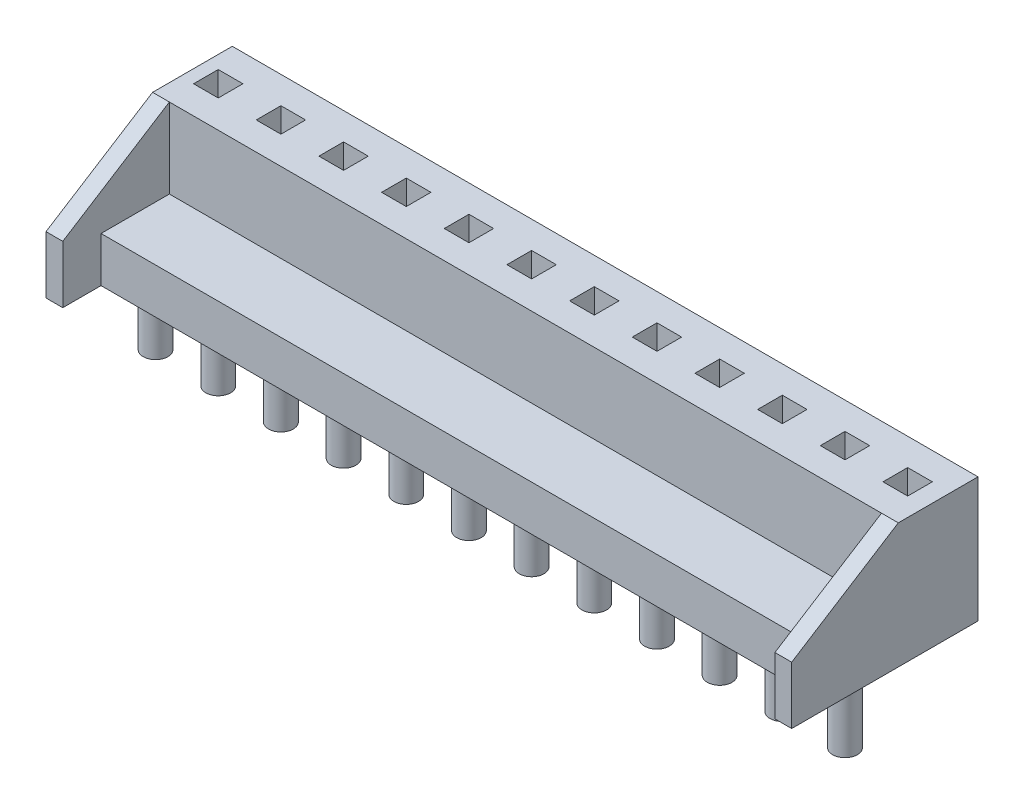
SolidWorks part; units mm, degrees
ref_plane "Front Plane" through (0, 0, 0) normal (0, 0, 1) x (1, 0, 0)
ref_plane "Top Plane" through (0, 0, 0) normal (0, 1, 0) x (1, 0, 0)
ref_plane "Right Plane" through (0, 0, 0) normal (1, 0, 0) x (0, 0, -1)
sketch "Sketch1" plane through (0, 0, 0) normal (1, 0, 0) x (0, 0, -1)
  line L0 (-2.77, 0) -> (3.23, 0)
  line L1 (3.23, 0) -> (3.23, 5.06)
  line L2 (3.23, 5.06) -> (0, 5.06)
  line L3 (0, 5.06) -> (0, 1.83)
  line L4 (0, 1.83) -> (-2.77, 1.83)
  line L5 (-2.77, 1.83) -> (-2.77, 0)
  dimension "D1" = 6
  dimension "D2" = 3.23
  dimension "D3" = 5.06
  dimension "D4" = 1.83
extrude "Boss-Extrude1" add sketch "Sketch1" along normal mid plane 30.22 contours L4 L5 L0 L1 L2 L3
sketch "Sketch2" plane through (15.11, 0, 0) normal (1, 0, 0) x (0, 0, -1)
  line L0 (-4.32, 0) -> (-4.32, 2.33)
  line L1 (-4.32, 2.33) -> (0, 5.06)
  line L2 (0, 5.06) -> (0, 0)
  line L3 (0, 0) -> (-4.32, 0)
  line L4 (3.23, 0) -> (3.23, 5.06) construction
  dimension "D1" = 7.55
  dimension "D2" = 2.33
extrude "Boss-Extrude2" add sketch "Sketch2" against normal blind 0.68
mirror "Mirror1" about plane through (0, 0, 0) normal (1, 0, 0) of "Boss-Extrude2"
sketch "Sketch3" plane through (0, 5.06, 0) normal (0, 1, 0) x (1, 0, 0)
  line L0 (15.11, 3.23) -> (15.11, 0) construction
  line L1 (14.36, 1.13) -> (13.36, 1.13)
  line L2 (14.36, 1.13) -> (14.36, 2.13)
  line L3 (14.36, 2.13) -> (13.36, 2.13)
  line L4 (13.36, 1.13) -> (13.36, 2.13)
  line L5 (15.11, 3.23) -> (-15.11, 3.23) construction
  dimension "D1" = 1
  dimension "D2" = 1
  dimension "D3" = 0.75
  dimension "D4" = 1.1
extrude "Cut-Extrude1" cut sketch "Sketch3" against normal through all
sketch "Sketch4" plane through (0, 0, 0) normal (0, 1, 0) x (1, 0, 0)
  line L0 (13.36, 1.13) -> (14.36, 1.13) construction
  line L1 (14.36, 1.13) -> (14.36, 2.13) construction
  circle A0 centre (13.86, -0.91) radius 0.5
  point P4 (13.86, 1.13)
  point P9 (14.36, 1.63)
  dimension "D2" = 1
  dimension "D1" = 2.54
extrude "Boss-Extrude3" add sketch "Sketch4" against normal blind 3
pattern_linear "LPattern1" count 12 spacing 2.54 along (-1, 0, 0) of "Cut-Extrude1", "Boss-Extrude3"
